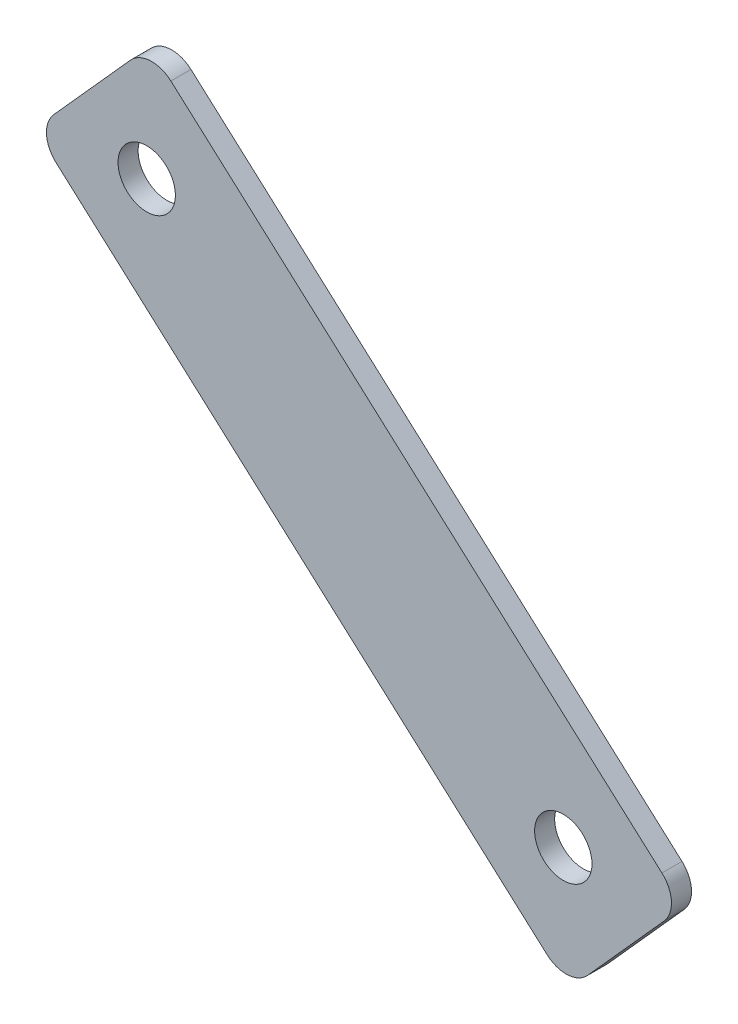
SolidWorks part; units mm, degrees
ref_plane "Front Plane" through (0, 0, 0) normal (0, 0, 1) x (1, 0, 0)
ref_plane "Top Plane" through (0, 0, 0) normal (0, 1, 0) x (1, 0, 0)
ref_plane "Right Plane" through (0, 0, 0) normal (1, 0, 0) x (0, 0, -1)
sketch "Sketch1" plane through (0, 0, 0) normal (0, 0, 1) x (1, 0, 0)
  line L0 (0, 0) -> (40.0588, 44.6687)
  line L1 (0, 0) -> (-186.1197, 166.9116)
  line L2 (40.0588, 44.6687) -> (-146.0609, 211.5803)
  line L3 (-186.1197, 166.9116) -> (-146.0609, 211.5803)
  dimension "D1" = 250
  dimension "D2" = 60
extrude "Boss-Extrude1" add sketch "Sketch1" along normal blind 7
fillet "Fillet1" radius 10 4 edges at (0, 0, 3.5) (40.0588, 44.6687, 3.5) (-186.1197, 166.9116, 3.5) (-146.0609, 211.5803, 3.5)
sketch "Sketch3" plane through (0, 0, 7) normal (0, 0, 1) x (1, 0, 0)
  circle A0 centre (-1.7786, 41.8917) radius 10
  circle A2 centre (-147.0418, 171.1527) radius 10
  point P4 (-146.7582, 170.5855)
  point P5 (-147.0418, 171.1527)
  point P10 (0, 0)
  dimension "D1" = 20
  dimension "D2" = 20
extrude "Cut-Extrude1" cut sketch "Sketch3" against normal blind 7
scale "Scale1" scale about centroid uniform scaling yes scale factor 0.2
scale "Scale2" scale about centroid uniform scaling yes scale factor 2.5
scale "Scale3" scale about centroid uniform scaling yes scale factor 0.8
